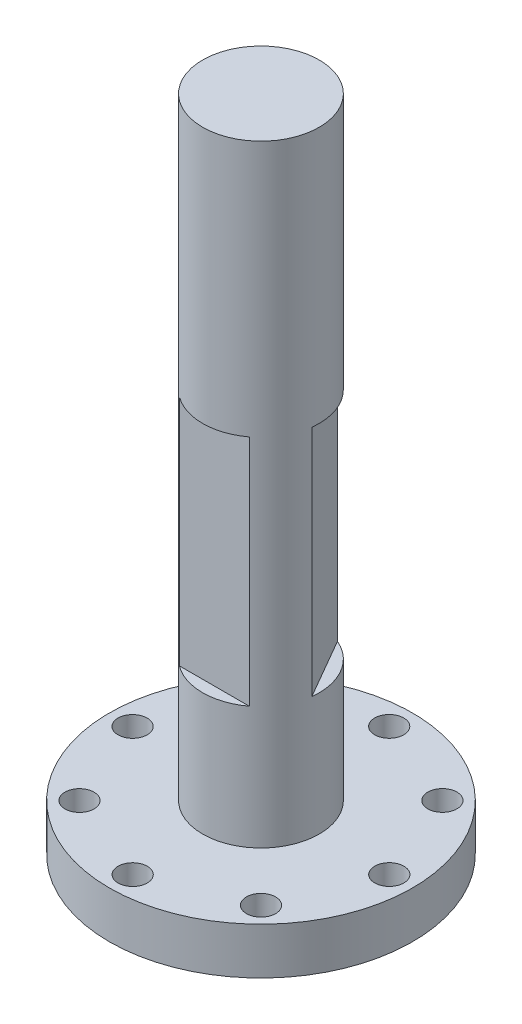
SolidWorks part; units mm, degrees
ref_plane "정면" through (0, 0, 0) normal (0, 0, 1) x (1, 0, 0)
ref_plane "윗면" through (0, 0, 0) normal (0, 1, 0) x (1, 0, 0)
ref_plane "우측면" through (0, 0, 0) normal (1, 0, 0) x (0, 0, -1)
sketch "스케치1" plane through (0, 0, 0) normal (0, 1, 0) x (1, 0, 0)
  circle A0 centre (0, 0) radius 13
  dimension "D1" = 26
extrude "보스-돌출1" add sketch "스케치1" along normal blind 4
sketch "스케치2" plane through (0, 4, 0) normal (0, 1, 0) x (1, 0, 0)
  circle A0 centre (0, 0) radius 5
  dimension "D1" = 10
extrude "보스-돌출2" add sketch "스케치2" along normal blind 52.5
sketch "스케치3" plane through (0, 4, 0) normal (0, 1, 0) x (1, 0, 0)
  line L0 (0, 0) -> (0, 50000) construction
  line L1 (0, 0) -> (50000, 0) construction
  line L2 (0, 0) -> (35355.3391, 35355.3391) construction
  line L3 (0, 0) -> (-35355.3391, 35355.3391) construction
  circle A0 centre (0, 11) radius 1.25
  circle A2 centre (7.7819, 7.7797) radius 1.25
  circle A3 centre (11.0074, 0) radius 1.25
  circle A4 centre (7.7871, -7.7819) radius 1.25
  circle A5 centre (0.0074, -11.0074) radius 1.25
  circle A6 centre (-7.7745, -7.7871) radius 1.25
  circle A7 centre (-11, -0.0074) radius 1.25
  circle A8 centre (-7.7797, 7.7745) radius 1.25
  point P17 (0.0037, -0.0037)
  dimension "D1" = 2.5
  dimension "D2" = 11
  dimension "D4" = 45
  dimension "D5" = 45
  dimension "D3" = 8
extrude "컷-돌출1" cut sketch "스케치3" against normal up to next
ref_plane "평면1" through (0, 0, 5) normal (0, 0, 1) x (1, 0, 0)
sketch "스케치4" plane through (0, 0, 5) normal (0, 0, 1) x (1, 0, 0)
  line L0 (0, -14.3) -> (0, 14.3) construction
  line L1 (-3, 34.5) -> (3, 34.5)
  line L2 (-3, 34.5) -> (-3, 14.5)
  line L3 (-3, 14.5) -> (3, 14.5)
  line L4 (3, 34.5) -> (3, 14.5)
  line L5 (13, 4) -> (-13, 4) construction
  dimension "D1" = 20
  dimension "D2" = 6
  dimension "D3" = 3
  dimension "D4" = 10.5
extrude "컷-돌출2" cut sketch "스케치4" against normal blind 1
ref_plane "평면2" through (4.3301, 0, -2.5) normal (0.866, 0, -0.5) x (0, -1, 0)
sketch "스케치5" plane through (4.3301, 0, -2.5) normal (0.866, 0, -0.5) x (0, -1, 0)
  line L0 (0, 0) -> (-50000, 0) construction
  line L1 (-34.5, 3) -> (-14.5, 3)
  line L2 (-34.5, 3) -> (-34.5, -3)
  line L3 (-34.5, -3) -> (-14.5, -3)
  line L4 (-14.5, 3) -> (-14.5, -3)
  line L5 (-4, 5) -> (-4, -5) construction
  dimension "D1" = 6
  dimension "D2" = 20
  dimension "D3" = 3
  dimension "D4" = 10.5
extrude "컷-돌출3" cut sketch "스케치5" against normal blind 1
sketch "스케치6" plane through (0, 0, 0) normal (0, -1, 0) x (1, 0, 0)
  circle A0 centre (0, 0) radius 6
  dimension "D1" = 12
extrude "컷-돌출5" cut sketch "스케치6" against normal blind 3 contours A0
sketch "스케치7" plane through (0, 3, 0) normal (0, -1, 0) x (1, 0, 0)
  circle A0 centre (0, 0) radius 3
  dimension "D1" = 6
extrude "컷-돌출6" cut sketch "스케치7" against normal blind 5
